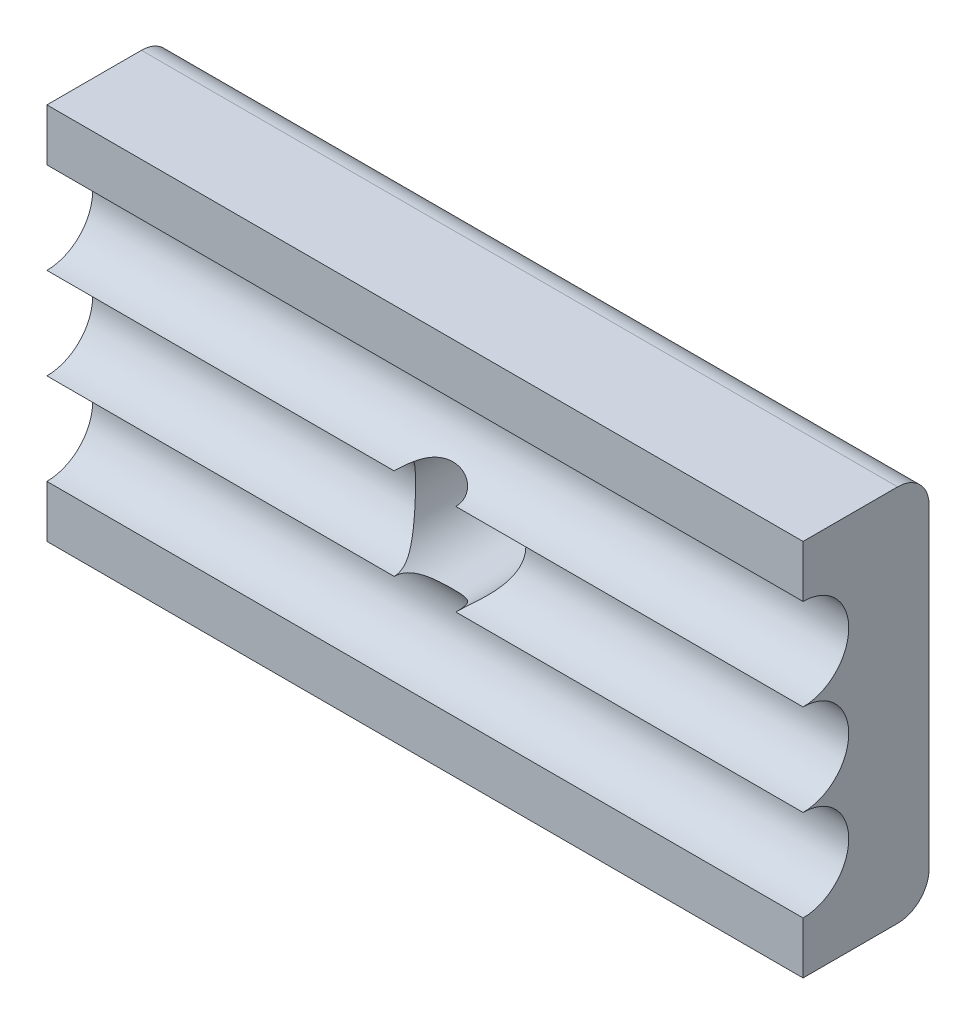
SolidWorks part; units mm, degrees
ref_plane "Front Plane" through (0, 0, 0) normal (0, 0, 1) x (1, 0, 0)
ref_plane "Top Plane" through (0, 0, 0) normal (0, 1, 0) x (1, 0, 0)
ref_plane "Right Plane" through (0, 0, 0) normal (1, 0, 0) x (0, 0, -1)
sketch "Sketch2" plane through (0, 0, 0) normal (0, 0, 1) x (1, 0, 0)
  line L1 (-5.0427, 4) -> (18.9573, 4)
  line L2 (-5.0427, 4) -> (-5.0427, -8)
  line L3 (-5.0427, -8) -> (18.9573, -8)
  line L4 (18.9573, 4) -> (18.9573, -8)
  dimension "D1" = 12
  dimension "D2" = 24
extrude "Boss-Extrude1" add sketch "Sketch2" along normal blind 4
sketch "Sketch3" plane through (0, 0, 4) normal (0, 0, 1) x (1, 0, 0)
  line L0 (-5.0427, 4) -> (-5.0427, -8) construction
  line L1 (18.9573, 4) -> (-5.0427, 4) construction
  circle A0 centre (6.9573, -2) radius 1.75
  point P5 (-5.0427, -2)
  point P8 (6.9573, 4)
  dimension "D1" = 3.5
extrude "Cut-Extrude1" cut sketch "Sketch3" against normal blind 5
sketch "Sketch4" plane through (-5.0427, 0, 0) normal (-1, 0, 0) x (0, 0, 1)
  line L0 (0, 4) -> (0, -8) construction
  line L1 (4, 4) -> (4, -8) construction
  circle A0 centre (4, -2) radius 1.45
  circle A2 centre (4, 0.9) radius 1.45
  circle A4 centre (4, -4.9) radius 1.45
  point P10 (0, -2)
  point P15 (4, -0.55)
  line M4 (4, -8) -> (4, 4)
  dimension "D1" = 2.9
  dimension "D2" = 2.9
  dimension "D3" = 2.9
fillet "Fillet1" radius 1 2 edges at (6.9573, -8, 0) (6.9573, 4, 0)
extrude "Cut-Extrude2" cut sketch "Sketch4" against normal blind 32 contours A4 M4 | A0 M4 | A2 M4
